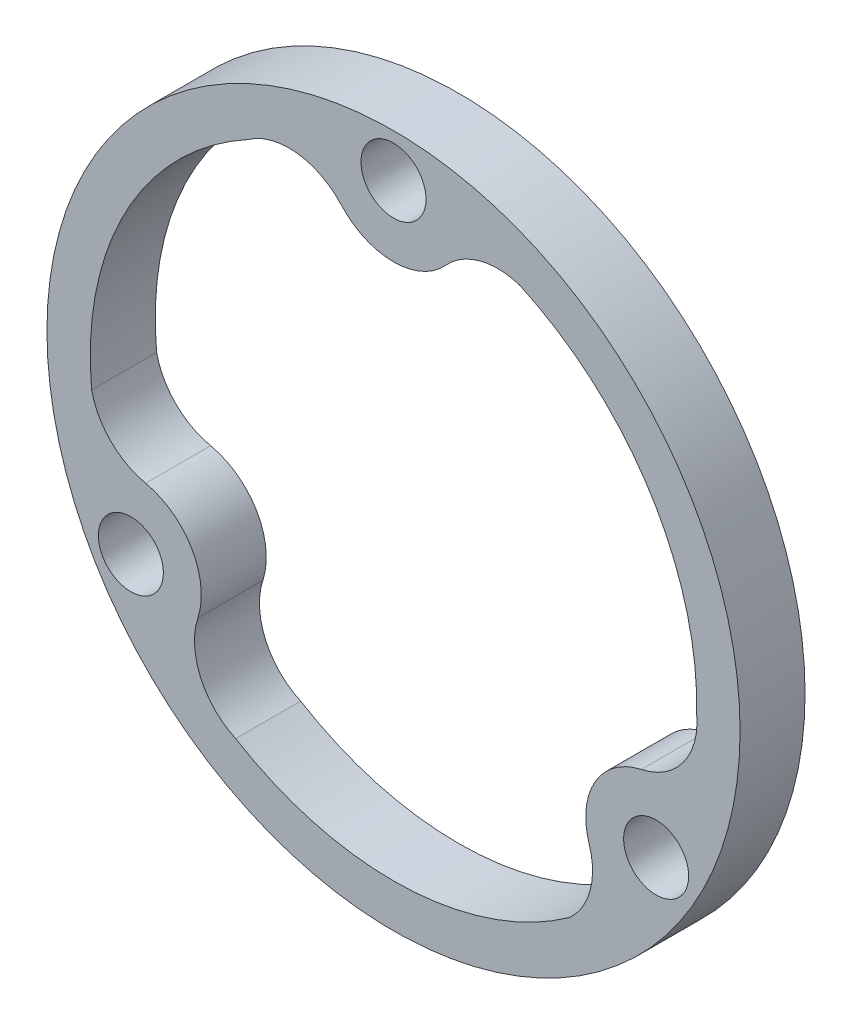
SolidWorks part; units mm, degrees
ref_plane "Plan de face" through (0, 0, 0) normal (0, 0, 1) x (1, 0, 0)
ref_plane "Plan de dessus" through (0, 0, 0) normal (0, 1, 0) x (1, 0, 0)
ref_plane "Plan de droite" through (0, 0, 0) normal (1, 0, 0) x (0, 0, -1)
sketch "Esquisse1" plane through (0, 0, 0) normal (0, 0, 1) x (1, 0, 0)
  line L0 (0, 14) -> (-12.125, -7.0011) construction
  line L1 (-12.125, -7.0011) -> (12.125, -7.0011) construction
  line L2 (12.125, -7.0011) -> (0, 14) construction
  circle A0 centre (0, 0) radius 16
  circle A2 centre (0, 14) radius 1.5
  arc A12 (-2.411, 11.8207) -> (2.411, 11.8207) centre (0, 14) ccw
  arc A16 (5.8094, 12.7378) -> (2.411, 11.8207) centre (4.8221, 9.6414) ccw
  arc A17 (-2.411, 11.8207) -> (-6.7074, 12.2887) centre (-4.8221, 9.6414) ccw
  arc A18 (-6.7074, 12.2887) -> (-13.9359, -1.3378) centre (0, 0) ccw
  arc A19 (8.1265, -11.4) -> (9.0315, -7.9984) centre (5.9386, -8.9967) ccw
  arc A20 (11.4425, -3.8223) -> (9.0315, -7.9984) centre (12.1244, -7) ccw
  arc A21 (11.4425, -3.8223) -> (13.996, -0.3356) centre (10.7607, -0.6447) ccw
  circle A22 centre (12.1244, -7) radius 1.5
  arc A23 (-13.9359, -1.3378) -> (-11.4425, -3.8223) centre (-10.7607, -0.6447) ccw
  arc A24 (-9.0315, -7.9984) -> (-11.4425, -3.8223) centre (-12.1244, -7) ccw
  arc A25 (-9.0315, -7.9984) -> (-7.2886, -11.9531) centre (-5.9386, -8.9967) ccw
  circle A26 centre (-12.1244, -7) radius 1.5
  arc A27 (-7.2886, -11.9531) -> (8.1265, -11.4) centre (0, 0) ccw
  arc A28 (13.996, -0.3356) -> (5.8094, 12.7378) centre (0, 0) ccw
  circle A29 centre (0, 14) radius 3.25 construction
  point P31 (0, 0)
  dimension "D1" = 32
  dimension "D2" = 3
  dimension "D3" = 3
  dimension "D4" = 6.5
  dimension "D5" = 14
  dimension "D8" = 14
  dimension "D9" = 3.25
  dimension "D10" = 14
  dimension "D11" = 3.25
  dimension "D12" = 24.25
  dimension "D13" = 24.25
  dimension "D6" = 60
  dimension "D7" = 60
  dimension "D14" = 10.78
  dimension "D15" = 10.78
extrude "Boss.-Extru.2" add sketch "Esquisse1" along normal blind 3
